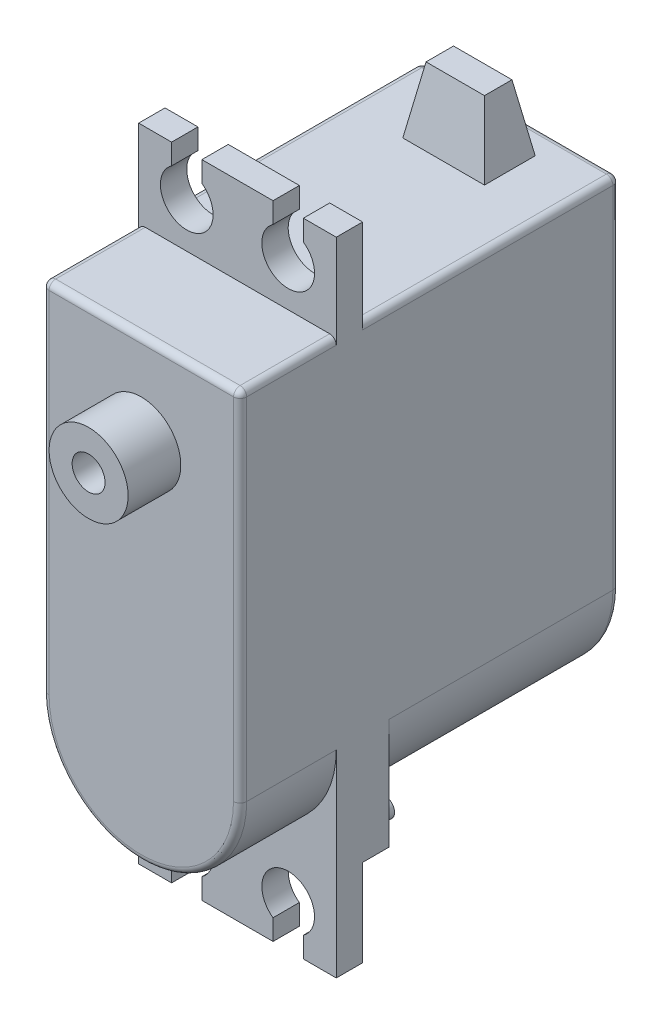
SolidWorks part; units mm, degrees
ref_plane "Front" through (0, 0, 0) normal (0, 0, 1) x (1, 0, 0)
ref_plane "Top" through (0, 0, 0) normal (0, 1, 0) x (1, 0, 0)
ref_plane "Right" through (0, 0, 0) normal (1, 0, 0) x (0, 0, -1)
sketch "Sketch2" plane through (0, 0, 0) normal (0, 0, 1) x (1, 0, 0)
  line L0 (45.1822, 0) -> (0, 0) construction
  line L1 (0, 0) -> (0, 54.1291) construction
  line L2 (-7.5, 7) -> (7.5, 7)
  line L3 (7.5, 7) -> (7.5, -20.1)
  line L4 (-7.5, 7) -> (-7.5, -20.1)
  circle A0 centre (0, 0) radius 3 construction
  arc A1 (7.5, -20.1) -> (-7.5, -20.1) centre (0, -20.1) cw
  point P10 (0, 0)
  point P11 (0, 0)
  point P13 (0, 7)
  dimension "D4" = 6
  dimension "D2" = 7
  dimension "D3" = 15
extrude "Boss-Extrude1" add sketch "Sketch2" against normal blind 28.8
sketch "Sketch3" plane through (0, 0, 0) normal (0, 0, 1) x (1, 0, 0)
  circle A0 centre (0, 0) radius 3 construction
  circle A1 centre (0, 0) radius 3
  circle A2 centre (0, 0) radius 1.25
  dimension "D1" = 2.5
extrude "Boss-Extrude2" add sketch "Sketch3" along normal blind 4
sketch "Sketch4" plane through (0, 0, 0) normal (1, 0, 0) x (0, 0, -1)
  line L0 (28.8, 7) -> (0, 7) construction
  line L2 (7.3, 7) -> (7.3, 13.6)
  line L3 (7.3, 13.6) -> (9.3, 13.6)
  line L4 (9.3, 7) -> (9.3, 13.6)
  line L10 (-3.4885, -10.75) -> (28.8, -10.75) construction
  line L11 (9.3, 7) -> (9.3, -35.1)
  line L12 (7.3, -35.1) -> (9.3, -35.1)
  line L13 (7.3, 7) -> (7.3, -35.1)
  line L18 (28.8, 7) -> (28.8, -20.1) construction
  line L19 (28.8, -20.1) -> (28.8, 7) construction
  line L20 (28.8, 7) -> (0, 7) construction
  point P13 (9.3, 7)
  dimension "D1" = 48.7
  dimension "D2" = 2
  dimension "D3" = 19.5
  dimension "D4" = 6.6
extrude "Boss-Extrude3" add sketch "Sketch4" along normal mid plane 15
sketch "Sketch5" plane through (0, 0, -9.3) normal (0, 0, -1) x (-1, 0, 0)
  line L1 (-7.5, -28.5) -> (7.5, -28.5)
  line L2 (-7.5, -28.5) -> (-7.5, -15.3294)
  line L3 (-7.5, -15.3294) -> (7.5, -15.3294)
  line L4 (7.5, -28.5) -> (7.5, -15.3294)
  line L5 (7.5, 7) -> (7.5, -20.1) construction
  line L6 (-7.5, -35.1) -> (7.5, -35.1) construction
  line L7 (-7.5, -20.1) -> (-7.5, 7) construction
  point P8 (0, 0)
  point P9 (-7.5, -15.3294)
  dimension "D1" = 6.6
extrude "Boss-Extrude4" add sketch "Sketch5" along normal blind 2
sketch "Sketch6" plane through (0, 0, -11.3) normal (0, 0, -1) x (-1, 0, 0)
  line L0 (0, -28.5) -> (0, -20.8508) construction
  line L1 (-7.5, -28.5) -> (7.5, -28.5) construction
  circle A0 centre (-6.2, -27) radius 0.725
  circle A1 centre (6.2, -27) radius 0.725
  dimension "D1" = 12.4
  dimension "D2" = 1.45
  dimension "D3" = 1.5
extrude "Boss-Extrude5" add sketch "Sketch6" along normal blind 1
sketch "Sketch7" plane through (0, 0, 0) normal (0, 0, 1) x (1, 0, 0)
  line L0 (-7.5, -10.75) -> (0, -10.75) construction
  line L1 (-7.5, 7) -> (-7.5, -20.1) construction
  line L2 (0, -10.75) -> (0, 13.6) construction
  line L3 (7.5, 13.6) -> (-7.5, 13.6) construction
  line L4 (0, -35.1) -> (0, -10.75) construction
  line L5 (7.5, -35.1) -> (-7.5, -35.1) construction
  line L6 (-5, 12.0363) -> (-5, 13.6)
  line L7 (-5, 13.6) -> (-2.7, 13.6)
  line L8 (-2.7, 13.6) -> (-2.7, 12.0363)
  line L9 (2.7, 13.6) -> (2.7, 12.0363)
  line L10 (5, 13.6) -> (2.7, 13.6)
  line L11 (5, 12.0363) -> (5, 13.6)
  line L12 (5, -33.5363) -> (5, -35.1)
  line L13 (5, -35.1) -> (2.7, -35.1)
  line L14 (2.7, -35.1) -> (2.7, -33.5363)
  line L15 (-2.7, -35.1) -> (-2.7, -33.5363)
  line L16 (-5, -35.1) -> (-2.7, -35.1)
  line L17 (-5, -33.5363) -> (-5, -35.1)
  arc A0 (-5, 12.0363) -> (-2.7, 12.0363) centre (-3.85, 10.4) ccw
  arc A4 (5, 12.0363) -> (2.7, 12.0363) centre (3.85, 10.4) cw
  arc A5 (5, -33.5363) -> (2.7, -33.5363) centre (3.85, -31.9) ccw
  arc A6 (-5, -33.5363) -> (-2.7, -33.5363) centre (-3.85, -31.9) cw
  point P1 (-2.7, 13.6)
  dimension "D1" = 7.7
  dimension "D2" = 4
  dimension "D3" = 42.3
  dimension "D4" = 2.3
extrude "Cut-Extrude1" cut sketch "Sketch7" against normal through all both and the other way through all
sketch "Sketch8" plane through (0, 7, 0) normal (0, 1, 0) x (1, 0, 0)
  line L0 (0, 26.8) -> (0, 28.8) construction
  line L1 (-3.1, 26.8) -> (3.1, 26.8)
  line L2 (-3.1, 26.8) -> (-3.1, 22.95)
  line L3 (-3.1, 22.95) -> (3.1, 22.95)
  line L4 (3.1, 26.8) -> (3.1, 22.95)
  line L5 (7.5, 28.8) -> (-7.5, 28.8) construction
  dimension "D1" = 6.2
  dimension "D2" = 3.85
  dimension "D3" = 2
extrude "Boss-Extrude6" add sketch "Sketch8" along normal blind 5 draft 10
fillet "Fillet1" radius 0.5 12 edges at (7.5, -6.55, 0) (0, 7, 0) (-7.5, -6.55, 0) (0, -27.6, 0) (7.5, -6.55, -28.8) (0, 7, -28.8) (-7.5, -6.55, -28.8) (0, -27.6, -28.8) (7.5, 7, -3.65) (7.5, 7, -19.05) (-7.5, 7, -19.05) (-7.5, 7, -3.65)
